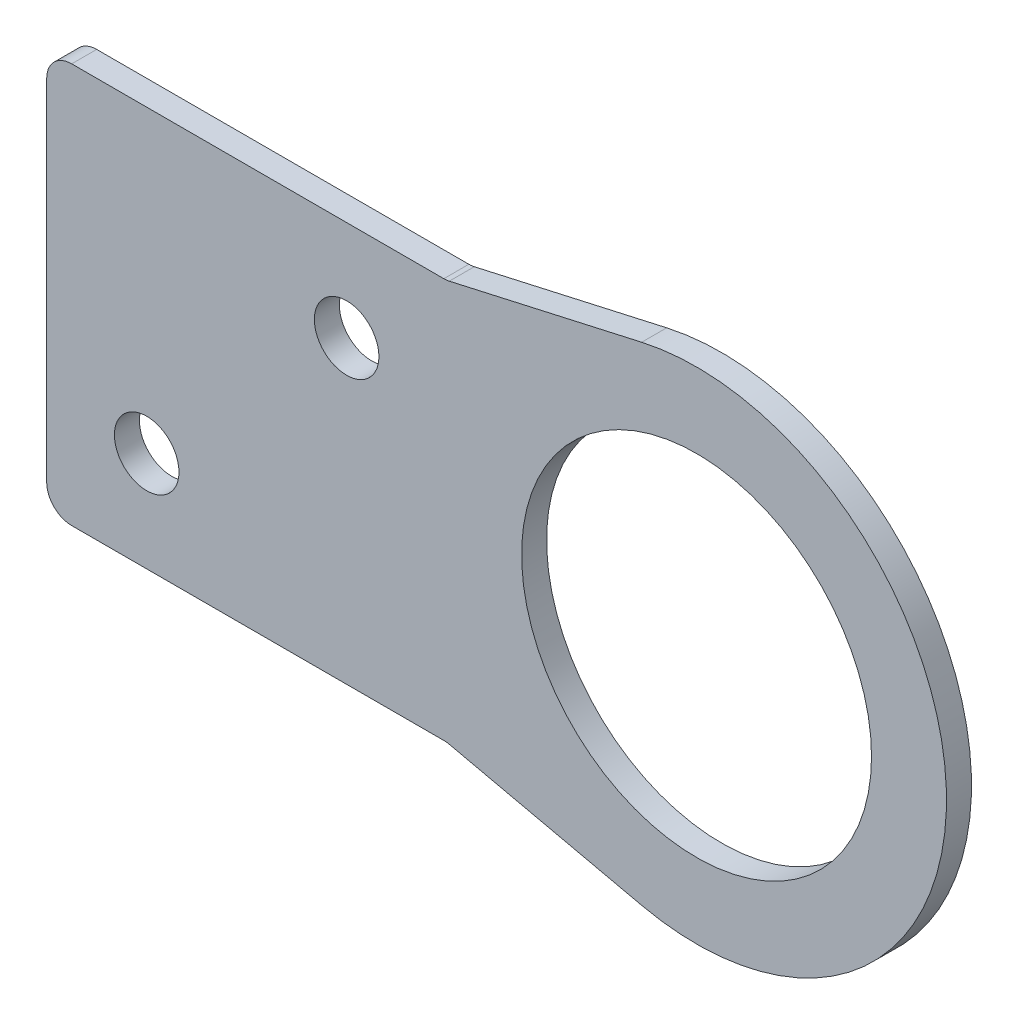
SolidWorks part; units mm, degrees
ref_plane "Front Plane" through (0, 0, 0) normal (0, 0, 1) x (1, 0, 0)
ref_plane "Top Plane" through (0, 0, 0) normal (0, 1, 0) x (1, 0, 0)
ref_plane "Right Plane" through (0, 0, 0) normal (1, 0, 0) x (0, 0, -1)
sketch "Sketch1" plane through (0, 0, 0) normal (0, 0, 1) x (1, 0, 0)
  line L0 (-174.625, 12.7) -> (-139.7, 12.7)
  line L1 (165.1, -12.7) -> (-165.1, -12.7)
  line L2 (165.1, -12.7) -> (165.1, 12.7)
  line L3 (165.1, 12.7) -> (-165.1, 12.7)
  line L4 (-165.1, -12.7) -> (-165.1, 12.7)
  line L5 (165.1, -12.7) -> (-165.1, 12.7) construction
  line L6 (165.1, 12.7) -> (-165.1, -12.7) construction
  line L7 (-139.7, 12.7) -> (-139.7, -12.7)
  line L8 (-139.7, -12.7) -> (-174.625, -12.7)
  line L9 (-165.1, 11.1125) -> (-88.6699, 11.1125) construction
  line L10 (-174.625, 12.7) -> (-174.625, 8) construction
  line L11 (0, 12.7) -> (0, -12.7) construction
  line L12 (139.7, 12.7) -> (139.7, -12.7)
  line L13 (165.1, 12.7) -> (177.4902, 15.4878)
  line L14 (165.1, -12.7) -> (177.4902, -15.4878)
  circle A0 centre (-174.625, 0) radius 8
  circle A1 centre (-174.625, 0) radius 12.7
  circle A2 centre (-158.75, 6.35) radius 2.05
  circle A3 centre (-146.05, -6.35) radius 2.05
  circle A7 centre (180.975, 0) radius 11.1125
  circle A8 centre (180.975, 0) radius 15.875
  circle A9 centre (146.05, -6.35) radius 2.05
  circle A10 centre (158.75, 6.35) radius 2.05
  point P0 (0, 0)
  dimension "D3" = 16
  dimension "D6" = 4.1
  dimension "D12" = 22.225
  dimension "D14" = 31.75
  dimension "D1" = 330.2
  dimension "D2" = 25.4
  dimension "D4" = 174.625
  dimension "D5" = 25.4
  dimension "D7" = 6.35
  dimension "D8" = 1.5875
  dimension "D9" = 6.35
  dimension "D10" = 6.35
  dimension "D11" = 6.35
  dimension "D13" = 180.975
extrude "Boss-Extrude1" add sketch "Sketch1" along normal blind 1.5875 contours L3 L12 L1 L2 A9 A10 | A8 L13 L2 | A8 A7 | A8 L2 L14
fillet "Fillet1" radius 1.5875 4 edges at (165.1, 12.7, 0.7937) (165.1, -12.7, 0.7937) (139.7, -12.7, 0.7937) (139.7, 12.7, 0.7937)
